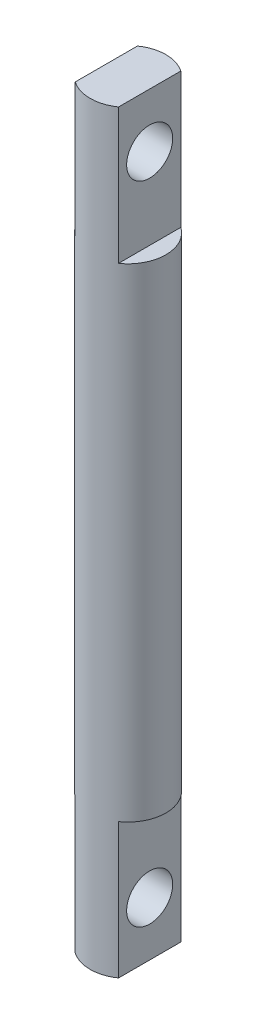
SolidWorks part; units mm, degrees
ref_plane "Front Plane" through (0, 0, 0) normal (0, 0, 1) x (1, 0, 0)
ref_plane "Top Plane" through (0, 0, 0) normal (0, 1, 0) x (1, 0, 0)
ref_plane "Right Plane" through (0, 0, 0) normal (1, 0, 0) x (0, 0, -1)
sketch "Sketch1" plane through (0, 0, 0) normal (0, 1, 0) x (1, 0, 0)
  circle A0 centre (0, 0) radius 7
  dimension "D1" = 14
extrude "Boss-Extrude1" add sketch "Sketch1" along normal blind 139.254
sketch "Sketch3" plane through (0, 0, 0) normal (0, -1, 0) x (1, 0, 0)
  line L0 (0, -7.7) -> (0, 7.7) construction
  line L1 (4, 9.0925) -> (7.8428, 9.0925)
  line L2 (4, 9.0925) -> (4, -10.2695)
  line L3 (4, -10.2695) -> (7.8428, -10.2695)
  line L4 (7.8428, 9.0925) -> (7.8428, -10.2695)
  line L5 (-4, 9.0925) -> (-7.6211, 9.0925)
  line L6 (-4, 9.0925) -> (-4, -10.2695)
  line L7 (-4, -10.2695) -> (-7.6211, -10.2695)
  line L8 (-7.6211, 9.0925) -> (-7.6211, -10.2695)
  dimension "D1" = 4
  dimension "D2" = 4
extrude "Cut-Extrude1" cut sketch "Sketch3" against normal blind 25
sketch "Sketch4" plane through (0, 139.254, 0) normal (0, 1, 0) x (1, 0, 0)
  line L0 (0, -7.7) -> (0, 7.7) construction
  line L1 (-4, 8.912) -> (-8.298, 8.912)
  line L2 (-4, 8.912) -> (-4, -9.7126)
  line L3 (-4, -9.7126) -> (-8.298, -9.7126)
  line L4 (-8.298, 8.912) -> (-8.298, -9.7126)
  line L5 (4, 8.912) -> (9.0565, 8.912)
  line L6 (4, 8.912) -> (4, -10.0919)
  line L7 (4, -10.0919) -> (9.0565, -10.0919)
  line L8 (9.0565, 8.912) -> (9.0565, -10.0919)
  dimension "D1" = 4
  dimension "D2" = 4
extrude "Cut-Extrude2" cut sketch "Sketch4" against normal blind 25
sketch "Sketch5" plane through (4, 0, 0) normal (1, 0, 0) x (0, 0, -1)
  line L0 (0, 0) -> (0, 139.254) construction
  line L1 (5.7446, 139.254) -> (-5.7446, 139.254) construction
  point P5 (0, 129.254)
  point P6 (0, 10)
  dimension "D1" = 10
  dimension "D2" = 10
hole_wizard "Tap Drill for M10x1.5 Tap1" positions "Sketch7" profile "Sketch6" hole size "M10x1.5" standard "ANSI Metric"
sketch "Sketch7" plane through (4, 0, 0) normal (1, 0, 0) x (0, 0, -1)
  point P0 (0, 129.254)
  point P3 (0, 10)
sketch "Sketch6" plane through (4, 129.254, 0) normal (0, 1, 0) x (0, 0, -1)
  line L0 (0, 0) -> (0, 22.5537)
  line L1 (0, 22.5537) -> (4.25, 20)
  line L2 (4.25, 20) -> (4.25, 0)
  line L5 (4.25, 0) -> (0, 0)
  line L10 (0, 22.5537) -> (-4.25, 20) construction
  line L11 (0, -6.35) -> (0, 107.95) construction
  dimension "Hole Dia." = 8.5
  dimension "Hole Depth" = 20
  dimension "Drill Angle" = 118
